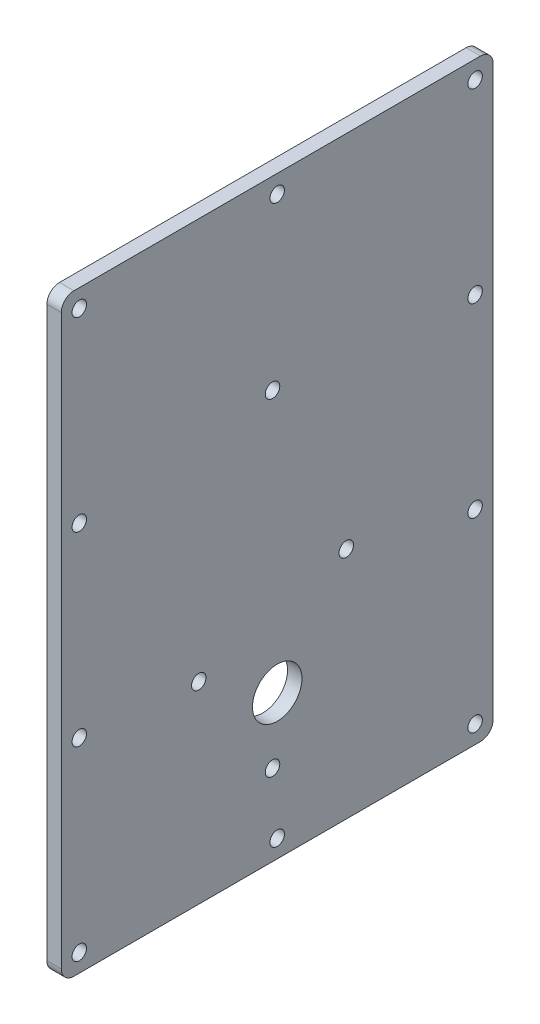
SolidWorks part; units mm, degrees
material "Acrylic (Medium-high impact)"
ref_plane "Front Plane" through (0, 0, 0) normal (0, 0, 1) x (1, 0, 0)
ref_plane "Top Plane" through (0, 0, 0) normal (0, 1, 0) x (1, 0, 0)
ref_plane "Right Plane" through (0, 0, 0) normal (1, 0, 0) x (0, 0, -1)
sketch "Sketch1" plane through (0, 0, 0) normal (1, 0, 0) x (0, 0, -1)
  line L1 (0, 0) -> (152.4, 0)
  line L2 (0, 0) -> (0, 209.55)
  line L3 (0, 209.55) -> (152.4, 209.55)
  line L4 (152.4, 0) -> (152.4, 209.55)
  dimension "D1" = 152.4
  dimension "D2" = 209.55
extrude "Boss-Extrude2" add sketch "Sketch1" along normal blind 5.08
sketch "Sketch2" plane through (5.08, 0, 0) normal (1, 0, 0) x (0, 0, -1)
  line L0 (0, 0) -> (152.4, 0) construction
  circle A3 centre (76.2, 50.8) radius 8.7313
  point P5 (76.2, 0)
  dimension "D1" = 50.8
  dimension "D2" = 17.4625
extrude "Cut-Extrude1" cut sketch "Sketch2" against normal through all
hole_wizard "#10 Clearance Hole2" positions "Sketch5" profile "Sketch6" hole size "#10" standard "ANSI Inch" end condition through all
sketch "Sketch5" plane through (5.08, 0, 0) normal (1, 0, 0) x (0, 0, -1)
  circle A8 centre (74.5554, 28.575) radius 2.8067 construction
  circle A9 centre (48.5204, 68.0466) radius 2.8067 construction
  circle A10 centre (74.5554, 144.107) radius 2.8067 construction
  circle A11 centre (100.5904, 82.55) radius 2.8067 construction
  circle A12 centre (74.5554, 28.575) radius 2.8067
  circle A13 centre (48.5204, 68.0466) radius 2.8067
  circle A14 centre (74.5554, 144.107) radius 2.8067
  circle A15 centre (100.5904, 82.55) radius 2.8067
  point P213 (48.5204, 68.0466)
  point P216 (74.5554, 144.107)
  point P219 (100.5904, 82.55)
  point P222 (74.5554, 28.575)
  point P235 (0, 0)
  point P236 (0, 0)
  point P237 (117.0162, 40.9218)
  point P238 (0, 0)
  point P239 (90.9812, -13.0532)
  point P240 (90.9812, 102.4787)
  point P241 (64.9462, 26.4184)
sketch "Sketch6" plane through (5.08, 68.0466, -48.5204) normal (0, 1, 0) x (0, 0, -1)
  line L0 (0, 0) -> (0, 5.08)
  line L1 (0, 5.08) -> (2.5527, 5.08)
  line L2 (2.5527, 5.08) -> (2.5527, 0)
  line L5 (2.5527, 0) -> (0, 0)
  line L11 (0, -6.35) -> (0, 107.95) construction
  dimension "Thru Hole Dia." = 5.1054
  dimension "Thru Hole Depth" = 5.08
fillet "Fillet1" radius 4.445 4 edges at (2.54, 0, 0) (2.54, 0, -152.4) (2.54, 209.55, -152.4) (2.54, 209.55, 0)
hole_wizard "#10 Clearance Hole1" positions "Sketch7" profile "Sketch8" hole size "#10" standard "ANSI Inch" end condition through all
sketch "Sketch7" plane through (5.08, 0, 0) normal (1, 0, 0) x (0, 0, -1)
  line L1 (6.35, 203.2) -> (146.05, 203.2)
  line L2 (6.35, 203.2) -> (6.35, 6.35)
  line L3 (6.35, 6.35) -> (146.05, 6.35)
  line L4 (146.05, 203.2) -> (146.05, 6.35)
  line L5 (6.35, 71.9667) -> (146.05, 71.9667) construction
  line L6 (6.35, 137.5833) -> (146.05, 137.5833) construction
  line L10 (76.2, 203.2) -> (76.2, 137.5833) construction
  line L11 (76.2, 137.5833) -> (76.2, 71.9667) construction
  line L12 (76.2, 71.9667) -> (76.2, 6.35) construction
  line L14 (147.955, 209.55) -> (4.445, 209.55) construction
  line L15 (4.445, 0) -> (147.955, 0) construction
  line L16 (0, 205.105) -> (0, 4.445) construction
  line L17 (152.4, 4.445) -> (152.4, 205.105) construction
  point P1 (6.35, 203.2)
  point P2 (146.05, 6.35)
  point P157 (6.35, 6.35)
  point P158 (146.05, 203.2)
  point P168 (76.2, 6.35)
  point P170 (76.2, 203.2)
  point P172 (6.35, 137.5833)
  point P174 (6.35, 71.9667)
  point P176 (146.05, 71.9667)
  point P179 (146.05, 137.5833)
  dimension "D1" = 6.35
  dimension "D2" = 6.35
  dimension "D3" = 6.35
  dimension "D4" = 6.35
sketch "Sketch8" plane through (5.08, 203.2, -6.35) normal (0, 1, 0) x (0, 0, -1)
  line L0 (0, 0) -> (0, 5.08)
  line L1 (0, 5.08) -> (2.5527, 5.08)
  line L2 (2.5527, 5.08) -> (2.5527, 0)
  line L5 (2.5527, 0) -> (0, 0)
  line L11 (0, -6.35) -> (0, 107.95) construction
  dimension "Thru Hole Dia." = 5.1054
  dimension "Thru Hole Depth" = 5.08
